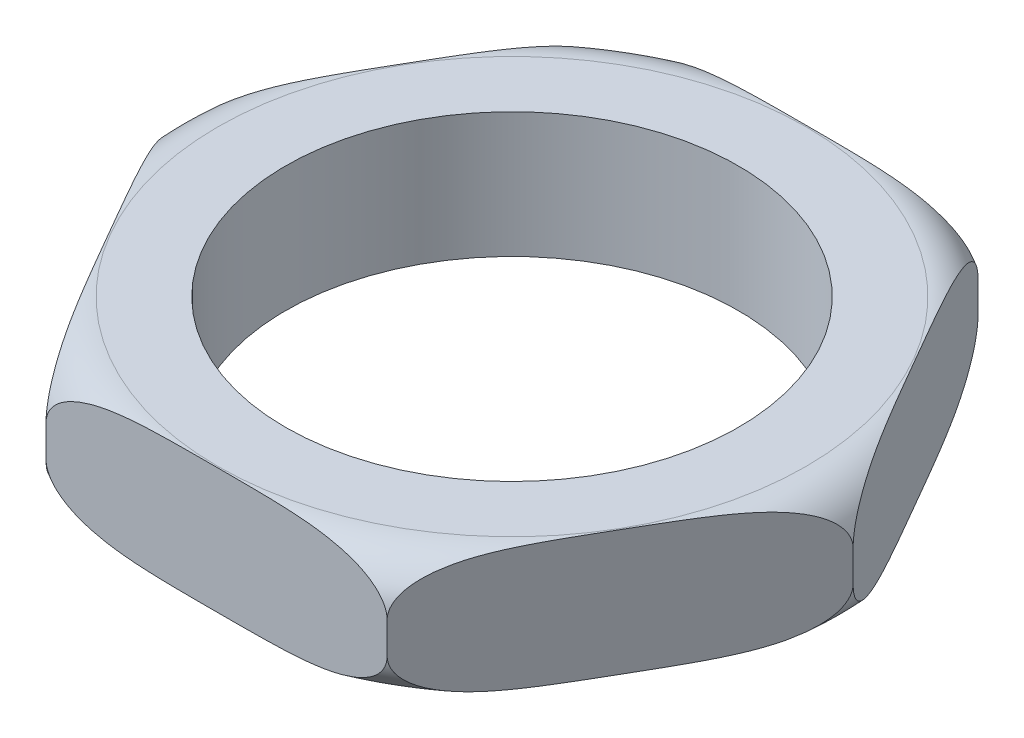
SolidWorks part; units mm, degrees
material "Chrome Stainless Steel"
ref_plane "Front" through (0, 0, 0) normal (0, 0, 1) x (1, 0, 0)
ref_plane "Top" through (0, 0, 0) normal (0, 1, 0) x (1, 0, 0)
ref_plane "Right" through (0, 0, 0) normal (1, 0, 0) x (0, 0, -1)
sketch "Sketch1" plane through (0, 0, 0) normal (0, 1, 0) x (1, 0, 0)
  line L1 (-2.7643, 4.7879) -> (-5.5286, 0)
  line L2 (-5.5286, 0) -> (-2.7643, -4.7879)
  line L3 (-2.7643, -4.7879) -> (2.7643, -4.7879)
  line L4 (2.7643, -4.7879) -> (5.5286, 0)
  line L5 (5.5286, 0) -> (2.7643, 4.7879)
  line L6 (2.7643, 4.7879) -> (-2.7643, 4.7879)
  circle A0 centre (0, 0) radius 4.7879 construction
  circle A1 centre (0, 0) radius 3.6703
  dimension "D2" = 7.3406
  dimension "D1" = 9.5758
extrude "Boss-Extrude1" add sketch "Sketch1" along normal blind 2.032
sketch "Sketch2" plane through (0, 0, 0) normal (0, 0, 1) x (1, 0, 0)
  line L0 (0, 0) -> (0, 3.0895) construction
  line L1 (4.7666, 2.032) -> (5.5286, 2.032)
  line L2 (2.7643, 2.032) -> (5.5286, 2.032) construction
  line L3 (5.5286, 2.032) -> (5.5286, 1.27)
  line L4 (5.5286, 2.032) -> (5.5286, 0) construction
  line L5 (4.7666, 0) -> (5.5286, 0)
  line L6 (2.7643, 0) -> (5.5286, 0) construction
  line L7 (5.5286, 0) -> (5.5286, 0.762)
  arc A0 (4.7666, 2.032) -> (5.5286, 1.27) centre (4.7666, 1.27) cw
  arc A1 (4.7666, 0) -> (5.5286, 0.762) centre (4.7666, 0.762) ccw
  dimension "D1" = 0.762
revolve "Cut-Revolve1" cut sketch "Sketch2" angle 360 about L0
